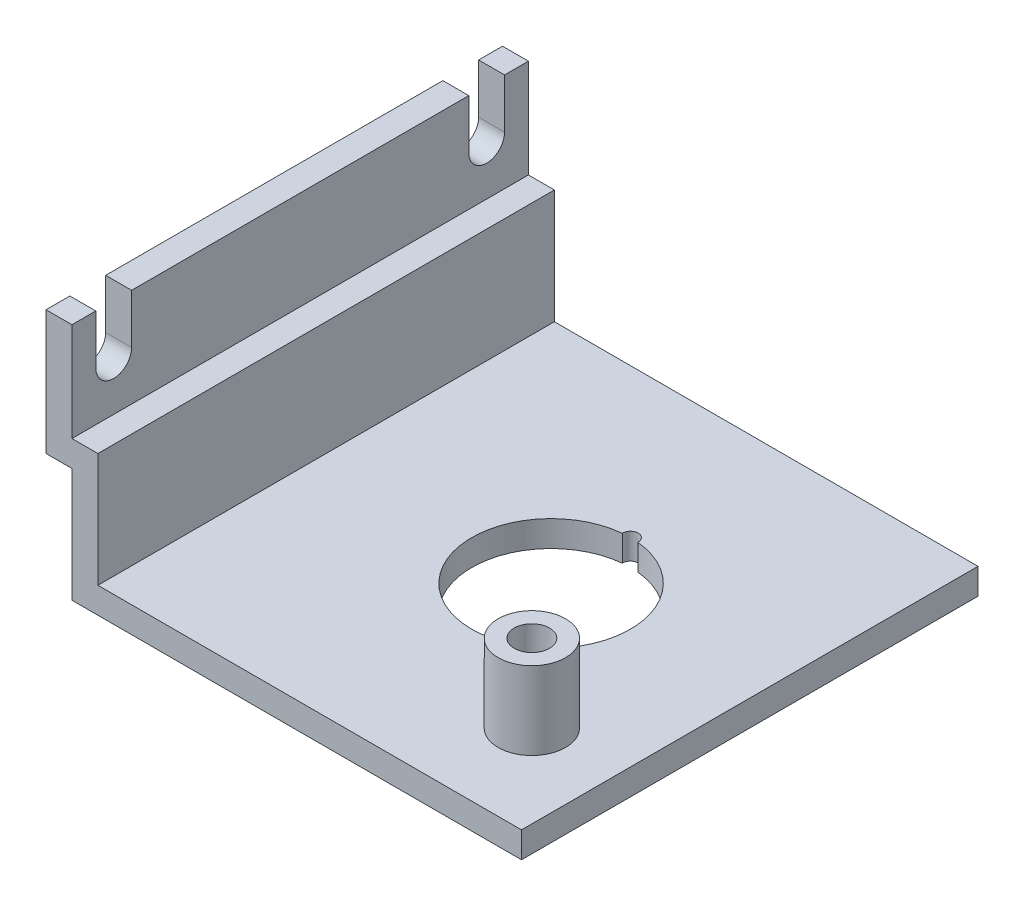
SolidWorks part; units mm, degrees
ref_plane "Přední rovina" through (0, 0, 0) normal (0, 0, 1) x (1, 0, 0)
ref_plane "Vrchní rovina" through (0, 0, 0) normal (0, 1, 0) x (1, 0, 0)
ref_plane "Pravá rovina" through (0, 0, 0) normal (1, 0, 0) x (0, 0, -1)
sketch "Skica1" plane through (0, 0, 0) normal (0, 0, 1) x (1, 0, 0)
  line L0 (0, 0) -> (0, 22)
  line L1 (0, 22) -> (-5, 22)
  line L2 (-5, 22) -> (-5, 46)
  line L3 (-5, 46) -> (0, 46)
  line L4 (0, 46) -> (0, 27)
  line L5 (0, 27) -> (5, 27)
  line L6 (5, 27) -> (5, 5)
  line L7 (5, 5) -> (86.66, 5)
  line L8 (86.66, 5) -> (86.66, 0)
  line L9 (86.66, 0) -> (0, 0)
  point P7 (0, 0)
  point P12 (0, 22.3585)
  point P13 (0, 21.6038)
  dimension "D1" = 5
  dimension "D2" = 24
  dimension "D3" = 27
  dimension "D4" = 5
  dimension "D5" = 86.66
extrude "Přidat vysunutím1" add sketch "Skica1" along normal blind 88
sketch "Skica2" plane through (-5, 0, 0) normal (-1, 0, 0) x (0, 0, 1)
  line L0 (44, 46) -> (44, 22) construction
  line L1 (88, 46) -> (0, 46) construction
  line L2 (88, 22) -> (0, 22) construction
  line L3 (4.6, 46) -> (4.6, 36.45)
  line L4 (11.5, 36.45) -> (11.5, 46)
  line L5 (0, 46) -> (0, 22) construction
  line L6 (4.6, 46) -> (11.5, 46)
  line L7 (83.4, 46) -> (76.5, 46)
  line L8 (76.5, 36.45) -> (76.5, 46)
  line L9 (83.4, 46) -> (83.4, 36.45)
  arc A0 (4.6, 36.45) -> (11.5, 36.45) centre (8.05, 36.45) ccw
  arc A1 (83.4, 36.45) -> (76.5, 36.45) centre (79.95, 36.45) cw
  dimension "D2" = 13
  dimension "D1" = 6.9
  dimension "D3" = 4.6
extrude "Odebrat vysunutím1" cut sketch "Skica2" against normal up to next
sketch "Skica3" plane through (0, 0, 0) normal (0, -1, 0) x (1, 0, 0)
  line L0 (86.66, 88) -> (86.66, 0) construction
  arc A0 (49.8582, 28.7735) -> (46.8618, 28.7735) centre (48.36, 44) ccw
  arc A1 (46.8618, 28.7735) -> (49.8582, 28.7735) centre (48.36, 28.7) ccw
  point P1 (50.4317, 59.2891)
  point P4 (86.66, 44)
  point P6 (0, 0)
  point P7 (0, 0)
  point P10 (48.36, 59.2265)
  point P11 (47.2936, 28.7061)
  point P12 (0, 0)
  dimension "D1" = 23
  dimension "D2" = 30.6
  dimension "D3" = 3
extrude "Odebrat vysunutím2" cut sketch "Skica3" against normal up to next
sketch "Skica4" plane through (0, 5, 0) normal (0, 1, 0) x (1, 0, 0)
  line L0 (86.66, -88) -> (86.66, 0) construction
  line L1 (86.66, -88) -> (5, -88) construction
  circle A0 centre (70.66, -70) radius 6.5
  dimension "D1" = 13
  dimension "D2" = 9.5
  dimension "D3" = 11.5
extrude "Přidat vysunutím2" add sketch "Skica4" along normal blind 15
hole_wizard "M8 závit1" positions "Skica5" profile "Skica6" tap size "M8" standard "ISO"
sketch "Skica5" plane through (0, 20, 0) normal (0, 1, 0) x (1, 0, 0)
  line L0 (70.66, -63.5) -> (70.66, -76.5) construction
  line L2 (64.16, -70) -> (77.16, -70) construction
  circle A0 centre (70.66, -70) radius 6.5 construction
  point P12 (70.66, -70)
sketch "Skica6" plane through (70.66, 20, 70) normal (1, 0, 0) x (0, 0, 1)
  line L0 (0, 0) -> (0, 16.0429)
  line L1 (0, 16.0429) -> (3.4, 14)
  line L2 (3.4, 14) -> (3.4, 0)
  line L5 (3.4, 0) -> (0, 0)
  line L10 (0, 16.0429) -> (-3.4, 14) construction
  line L11 (0, -6.35) -> (0, 107.95) construction
  dimension "Průměr závitníku" = 6.8
  dimension "Hloubka závitníku" = 14
  dimension "Úhel vrtání" = 118
cosmetic thread "Závit díry1" parameters "D1"=12, "D2"=8
